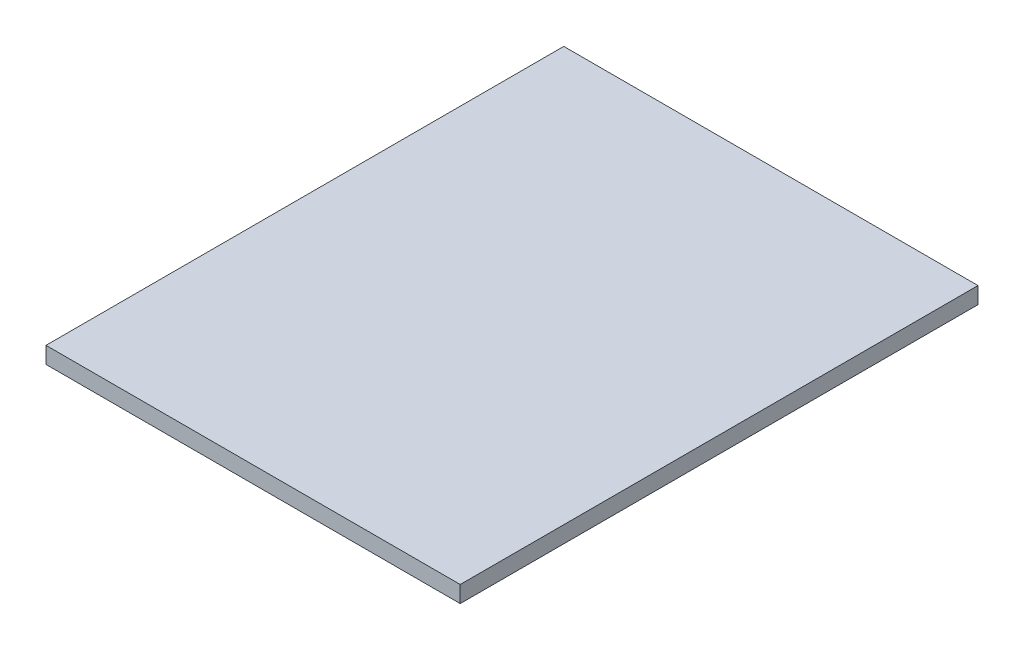
SolidWorks part; units mm, degrees
material "1060 Alloy"
ref_plane "Front Plane" through (0, 0, 0) normal (0, 0, 1) x (1, 0, 0)
ref_plane "Top Plane" through (0, 0, 0) normal (0, 1, 0) x (1, 0, 0)
ref_plane "Right Plane" through (0, 0, 0) normal (1, 0, 0) x (0, 0, -1)
sketch "Sketch1" plane through (0, 0, 0) normal (0, 1, 0) x (1, 0, 0)
  line L1 (0, 0) -> (101.6, 0)
  line L2 (0, 0) -> (0, 127)
  line L3 (0, 127) -> (101.6, 127)
  line L4 (101.6, 0) -> (101.6, 127)
  dimension "D1" = 127
  dimension "D2" = 101.6
extrude "Boss-Extrude1" add sketch "Sketch1" along normal blind 4.064
